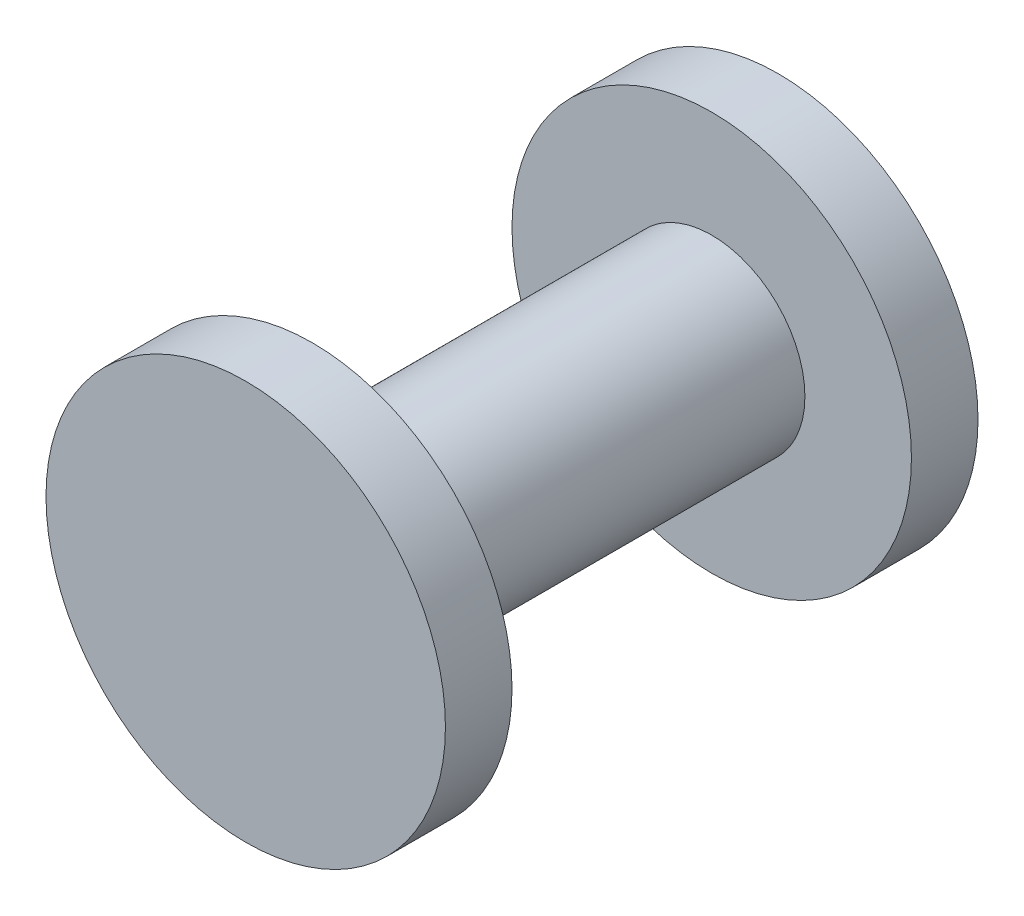
SolidWorks part; units mm, degrees
ref_plane "前视基准面" through (0, 0, 0) normal (0, 0, 1) x (1, 0, 0)
ref_plane "上视基准面" through (0, 0, 0) normal (0, 1, 0) x (1, 0, 0)
ref_plane "右视基准面" through (0, 0, 0) normal (1, 0, 0) x (0, 0, -1)
sketch "草图1" plane through (0, 0, 0) normal (0, 0, 1) x (1, 0, 0)
  circle A0 centre (0, 0) radius 14
  circle A1 centre (0, 0) radius 30
  dimension "D1" = 28
  dimension "D2" = 60
extrude "凸台-拉伸1" add sketch "草图1" along normal blind 10
sketch "草图2" plane through (0, 0, 10) normal (0, 0, 1) x (1, 0, 0)
  circle A0 centre (0, 0) radius 14 construction
  circle A1 centre (0, 0) radius 14
extrude "凸台-拉伸2" add sketch "草图2" along normal blind 70 and the other way up to vertex (10 mm away) other way up to point (0, 0, 0)
sketch "草图3" plane through (0, 0, 80) normal (0, 0, 1) x (1, 0, 0)
  circle A1 centre (0, 0) radius 30
  circle A2 centre (0, 0) radius 30
  circle A3 centre (0, 0) radius 14
  circle A4 centre (0, 0) radius 14
  dimension "D1" = 0
  dimension "D2" = 0
extrude "凸台-拉伸3" add sketch "草图3" against normal blind 10
